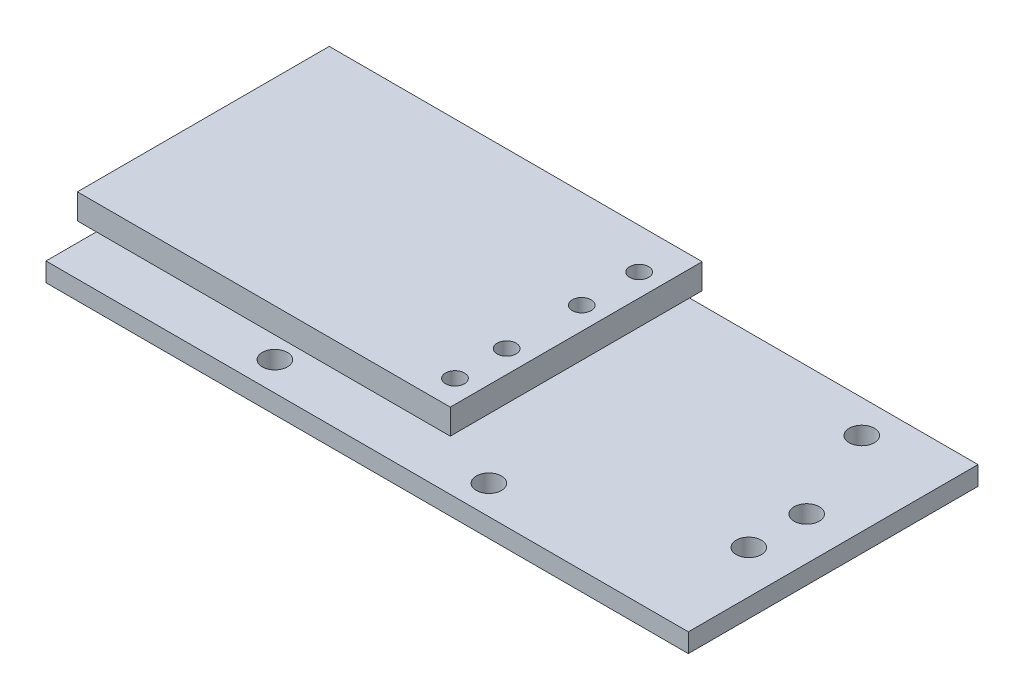
SolidWorks part; units mm, degrees
material "Плата системы питания"
ref_plane "Спереди" through (0, 0, 0) normal (0, 0, 1) x (1, 0, 0)
ref_plane "Сверху" through (0, 0, 0) normal (0, 1, 0) x (1, 0, 0)
ref_plane "Справа" through (0, 0, 0) normal (1, 0, 0) x (0, 0, -1)
sketch "Эскиз1" plane through (0, 0, 0) normal (0, 1, 0) x (1, 0, 0)
  line L0 (-25.5, 11.5) -> (25.5, 11.5)
  line L1 (-25.5, 11.5) -> (-25.5, -11.5)
  line L2 (25.5, 11.5) -> (25.5, -11.5)
  line L3 (-25.5, -11.5) -> (25.5, -11.5)
  line L4 (-25.5, 11.5) -> (25.5, -11.5) construction
  line L5 (25.5, 11.5) -> (-25.5, -11.5) construction
  circle A0 centre (-18.5986, 8.8859) radius 0.5
  circle A1 centre (18.8867, 8.8859) radius 1
  circle A2 centre (22.0956, -3.2932) radius 1
  circle A3 centre (22.0956, 1.3013) radius 1
  circle A4 centre (7.364, -9.2004) radius 1
  circle A5 centre (-9.6283, -9.2004) radius 1
  point P1 (0, 0)
extrude "Бобышка-Вытянуть1" add sketch "Эскиз1" along normal blind 1.5
sketch "Эскиз2" plane through (0, 1.5, 0) normal (0, 1, 0) x (1, 0, 0)
  line L0 (-4.0317, -6.7891) -> (-22.2905, -6.7891)
  line L1 (-4.0317, -6.7891) -> (-4.0317, 6.7891)
  line L2 (-22.2905, -6.7891) -> (-22.2905, 6.7891)
  line L3 (-4.0317, 6.7891) -> (-22.2905, 6.7891)
  line L4 (-4.0317, -6.7891) -> (-22.2905, 6.7891) construction
  line L5 (-22.2905, -6.7891) -> (-4.0317, 6.7891) construction
  point P1 (-13.1611, 0)
extrude "Бобышка-Вытянуть2" add sketch "Эскиз2" along normal blind 2.5
sketch "Эскиз3" plane through (0, 4, 0) normal (0, 1, 0) x (1, 0, 0)
  line L0 (-4.0317, -6.7891) -> (-22.2905, -6.7891)
  line L1 (-22.2905, -6.7891) -> (-22.2905, 6.7891)
  line L2 (-4.0317, 6.7891) -> (-22.2905, 6.7891) construction
  line L3 (-22.2905, 6.7891) -> (-22.2905, -6.7891) construction
  line L4 (-22.2905, 6.7891) -> (-4.0317, -6.7891)
  line L5 (-22.2905, -6.7891) -> (-13.1611, 0)
  line L6 (-13.1611, 0) -> (-4.0317, 6.7891)
  line L7 (-4.0317, 6.7891) -> (-22.2905, 6.7891)
  line L8 (-4.0317, 6.7891) -> (-4.0317, -6.7891)
  line L9 (-13.1611, 0) -> (-4.0317, 0)
  line L10 (5.0976, -10) -> (-24.5111, -10)
  line L11 (5.0976, -10) -> (5.0976, 10)
  line L12 (-24.5111, -10) -> (-24.5111, 10)
  line L13 (5.0976, 10) -> (-24.5111, 10)
  line L14 (5.0976, -10) -> (-24.5111, 10) construction
  line L15 (-24.5111, -10) -> (5.0976, 10) construction
  circle A0 centre (3.3082, -7.8368) radius 0.75
  circle A1 centre (3.3082, -3.7336) radius 0.75
  circle A2 centre (3.3082, 2.2268) radius 0.75
  circle A3 centre (3.3082, 6.7891) radius 0.75
  point P14 (-9.7068, 0)
  line M3 (-4.0317, -6.7891) -> (-4.0317, 6.7891)
  line M4 (-4.0317, 6.7891) -> (-22.2905, 6.7891)
  line M5 (-22.2905, 6.7891) -> (-22.2905, -6.7891)
  line M6 (-22.2905, -6.7891) -> (-4.0317, -6.7891)
extrude "Бобышка-Вытянуть3" add sketch "Эскиз3" along normal blind 2 contours L6 L9 L8 | L9 L4 M3 | L5 L4 M6 | L5 L4 M5 | L4 L6 M4 | L11 L13 L12 L10 A3 A2 A1 A0 L8 M3 M6 M5 M4
